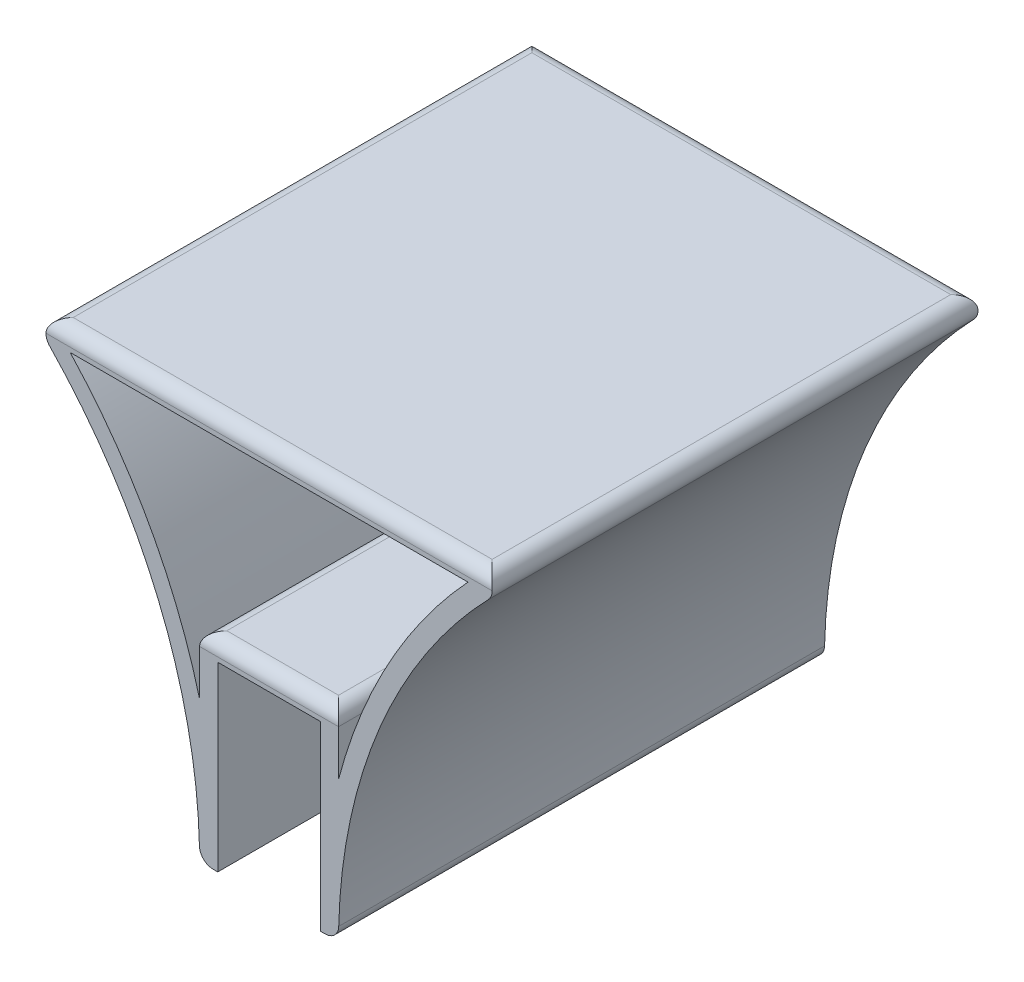
SolidWorks part; units mm, degrees
ref_plane "Plan de face" through (0, 0, 0) normal (0, 0, 1) x (1, 0, 0)
ref_plane "Plan de dessus" through (0, 0, 0) normal (0, 1, 0) x (1, 0, 0)
ref_plane "Plan de droite" through (0, 0, 0) normal (1, 0, 0) x (0, 0, -1)
sketch "Esquisse1" plane through (0, 0, 0) normal (0, 0, 1) x (1, 0, 0)
  line L0 (-11.3, 0) -> (11.3, 0)
  line L1 (11.3, 0) -> (11.3, -40)
  line L2 (11.3, -40) -> (15.3, -40)
  line L3 (53.5, 46.8304) -> (-53.5, 46.8304)
  line L4 (0, -55) -> (0, 55) construction
  line L5 (-11.3, -40) -> (-15.3, -40)
  line L6 (-11.3, 0) -> (-11.3, -40)
  line L7 (43.8062, 42.8304) -> (-43.8062, 42.8304)
  line L8 (-15.3, -9.0439) -> (-15.3, -9.0439)
  line L9 (-15.3, 4) -> (-15.3, -9.0439)
  line L10 (-15.3, 4) -> (15.3, 4)
  line L11 (15.3, 4) -> (15.3, -9.0439)
  line L12 (15.3, -9.0439) -> (15.3, -9.0439)
  arc A0 (15.3, -40) -> (53.5, 46.8304) centre (133.0848, -40) cw
  arc A1 (-15.3, -40) -> (-53.5, 46.8304) centre (-133.0848, -40) ccw
  arc A2 (-15.3, -9.0439) -> (-43.8062, 42.8304) centre (-133.0848, -40) ccw
  arc A3 (15.3, -9.0439) -> (43.8062, 42.8304) centre (133.0848, -40) cw
  point P0 (13.7193, -18.8289)
  point P13 (0, 46.8304)
  point P15 (0, 0)
  dimension "D1" = 22.6
  dimension "D2" = 107
  dimension "D3" = 4
  dimension "D4" = 40
  dimension "D5" = 4
extrude "Boss.-Extru.1" add sketch "Esquisse1" against normal mid plane 107
fillet "Congé1" radius 3 10 edges at (-53.5, 46.8304, 0) (0, 46.8304, -53.5) (53.5, 46.8304, 0) (0, 46.8304, 53.5) (-15.3, 4, 0) (0, 4, -53.5) (15.3, 4, 0) (0, 4, 53.5) (-15.3, -40, 0) (15.3, -40, 0)
